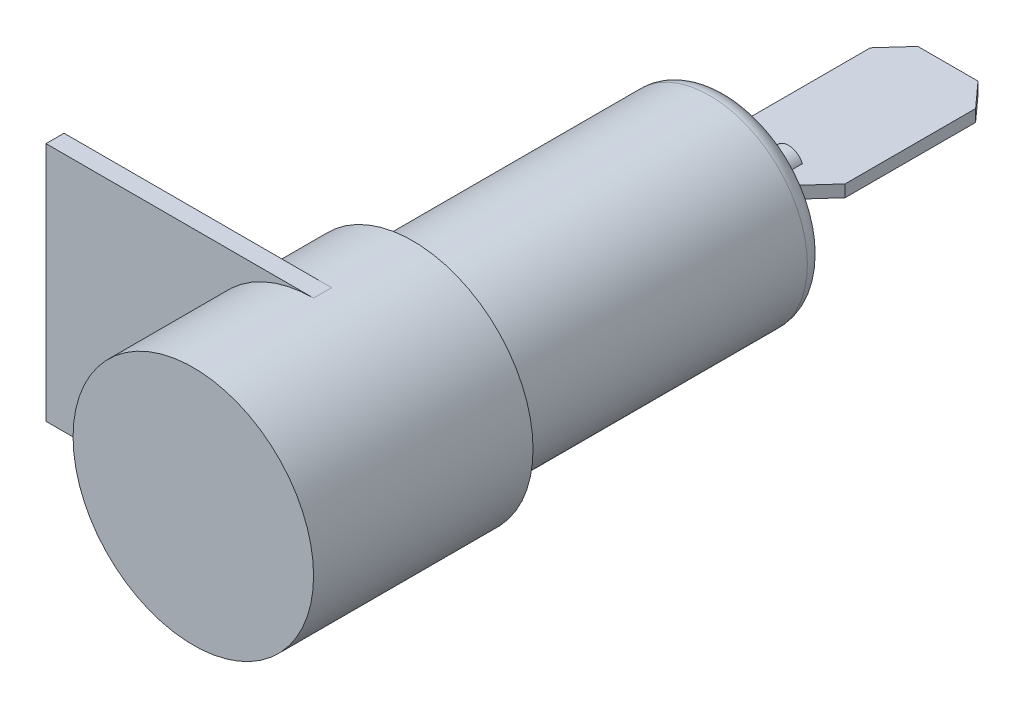
SolidWorks part; units mm, degrees
ref_plane "Front Plane" through (0, 0, 0) normal (0, 0, 1) x (1, 0, 0)
ref_plane "Top Plane" through (0, 0, 0) normal (0, 1, 0) x (1, 0, 0)
ref_plane "Right Plane" through (0, 0, 0) normal (1, 0, 0) x (0, 0, -1)
sketch "Sketch2" plane through (0, 0, 0) normal (0, 1, 0) x (1, 0, 0)
  line L0 (0, -8) -> (-8, -8)
  line L1 (-8, -8) -> (-8, 6.6)
  line L2 (-8, 6.6) -> (-6.5, 6.8)
  line L3 (-6.5, 6.8) -> (-6.5, 26.35)
  line L4 (-5.25, 27.6) -> (-1, 27.6)
  line L5 (0, -8) -> (0, 46.0792) construction
  line L6 (0, -8) -> (0, 31.6)
  line L7 (-1, 27.6) -> (-1, 31.6)
  line L8 (-1, 31.6) -> (0, 31.6)
  arc A0 (-5.25, 27.6) -> (-6.5, 26.35) centre (-5.25, 26.35) ccw
  dimension "D6" = 1.25
  dimension "D1" = 35.6
  dimension "D2" = 13
  dimension "D3" = 16
  dimension "D4" = 14.6
  dimension "D5" = 14.8
  dimension "D7" = 8
  dimension "D8" = 4
  dimension "D9" = 2
revolve "Revolve1" add sketch "Sketch2" angle 360 about L5
sketch "Sketch3" plane through (0, 0, 0) normal (0, 0, 1) x (1, 0, 0)
  line L1 (0, -8) -> (-17.8, -8)
  line L2 (0, -8) -> (0, 8)
  line L3 (0, 8) -> (-17.8, 8)
  line L4 (-17.8, -8) -> (-17.8, 8)
  circle A0 centre (0, 0) radius 8 construction
  dimension "D1" = 17.8
extrude "Boss-Extrude1" add sketch "Sketch3" against normal blind 1.2
sketch "Sketch5" plane through (0, 0, 0) normal (0, 1, 0) x (1, 0, 0)
  line L0 (-2, 30.2) -> (2, 30.2)
  line L3 (3.5, 40.5401) -> (2, 42.2)
  line L4 (2, 42.2) -> (-2, 42.2)
  line L7 (-3.5, 31.8599) -> (-2, 30.2)
  line L8 (5.25, 27.6) -> (-5.25, 27.6) construction
  line L9 (-3.5, 31.8599) -> (-3.5, 40.5401)
  line L10 (-3.5, 40.5401) -> (-2, 42.2)
  line L11 (3.5, 40.5401) -> (3.5, 31.8599)
  line L12 (3.5, 31.8599) -> (2, 30.2)
  line L13 (0, 0) -> (0, 42.2) construction
  dimension "D1" = 2.6
  dimension "D2" = 12
  dimension "D3" = 7
  dimension "D4" = 4
extrude "Boss-Extrude2" add sketch "Sketch5" along normal mid plane 0.8
